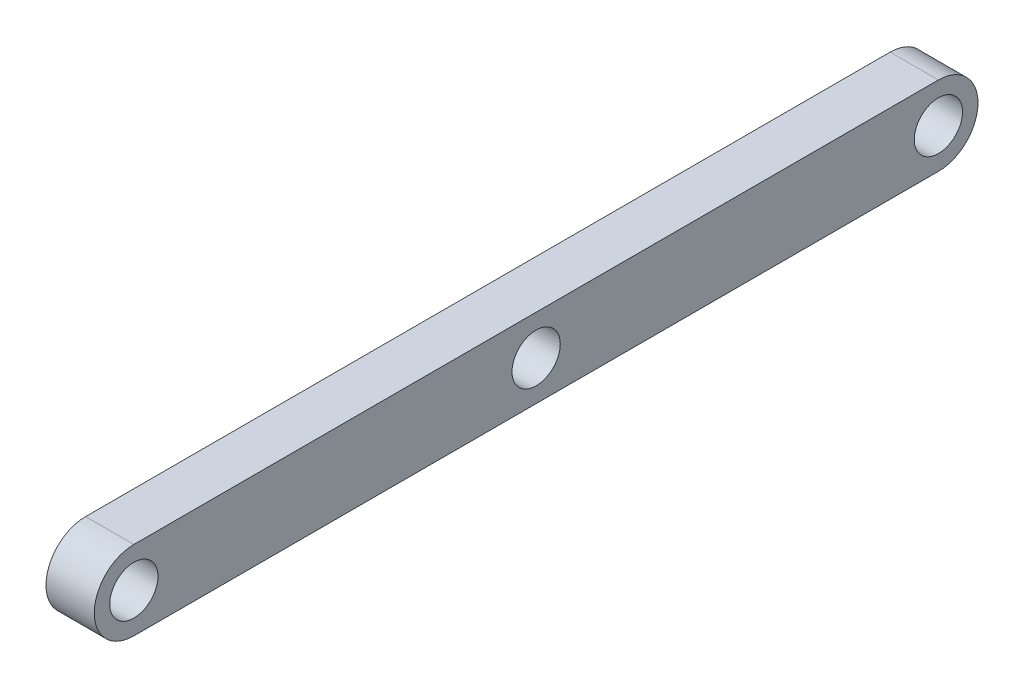
SolidWorks part; units mm, degrees
material "Cast Alloy Steel"
ref_plane "Front Plane" through (0, 0, 0) normal (0, 0, 1) x (1, 0, 0)
ref_plane "Top Plane" through (0, 0, 0) normal (0, 1, 0) x (1, 0, 0)
ref_plane "Right Plane" through (0, 0, 0) normal (1, 0, 0) x (0, 0, -1)
sketch "Sketch1" plane through (0, 0, 0) normal (1, 0, 0) x (0, 0, -1)
  line L0 (-48.8786, 0) -> (451.1214, 0) construction
  line L2 (-48.8786, 24.6078) -> (451.1214, 24.6078)
  line L3 (-48.8786, -24.6078) -> (451.1214, -24.6078)
  arc A0 (-48.8786, 24.6078) -> (-48.8786, -24.6078) centre (-48.8786, 0) ccw
  arc A1 (451.1214, -24.6078) -> (451.1214, 24.6078) centre (451.1214, 0) ccw
  circle A2 centre (-48.8786, 0) radius 15
  circle A3 centre (451.1214, 0) radius 15
  circle A4 centre (201.1214, 0) radius 15
  point P5 (201.1214, 0)
  dimension "D1" = 30
  dimension "D2" = 30
  dimension "D3" = 30
extrude "Boss-Extrude1" add sketch "Sketch1" along normal blind 30
